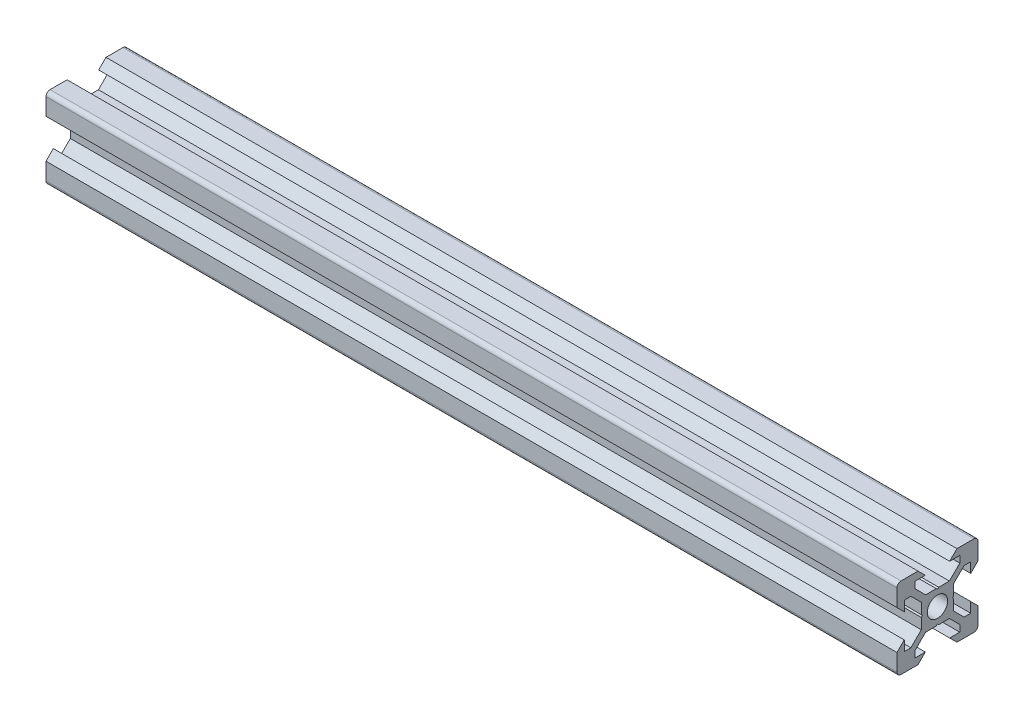
SolidWorks part; units mm, degrees
material "6063-T5"
material "6063-T5"
ref_plane "Plano frontal" through (0, 0, 0) normal (0, 0, 1) x (1, 0, 0)
ref_plane "Plano superior" through (0, 0, 0) normal (0, 1, 0) x (1, 0, 0)
ref_plane "Plano direito" through (0, 0, 0) normal (1, 0, 0) x (0, 0, -1)
sketch "Esboço1" plane through (0, 0, 0) normal (0, 0, 1) x (1, 0, 0)
  line L0 (0, 0) -> (210, 0)
  dimension "D1" = 210
other "Quadrado PF20-11 - PERFIL 2020 V-SLOT(1)"
ref_plane "Plano1" through (0, 0, 0) normal (1, 0, 0) x (0, 1, 0)
sketch "Sketch11" plane through (0, 0, 0) normal (1, 0, 0) x (0, 1, 0)
  line L0 (-4.8, 10) -> (-3, 8.2)
  line L1 (-3, 8.2) -> (-5.5, 8.2)
  line L2 (-5.5, 8.2) -> (-5.5, 6.5607)
  line L3 (-5.5, 6.5607) -> (-2.9393, 4)
  line L4 (-2.9393, 4) -> (-0.3, 4)
  line L5 (5.5, 6.5607) -> (2.9393, 4)
  line L6 (5.5, 8.2) -> (5.5, 6.5607)
  line L7 (3, 8.2) -> (5.5, 8.2)
  line L8 (4.8, 10) -> (3, 8.2)
  line L9 (-0.3, 4) -> (0, 3.7)
  line L10 (0.3, 4) -> (0, 3.7)
  line L11 (0.3, 4) -> (2.9393, 4)
  line L12 (9, 10) -> (4.8, 10)
  line L13 (10, 4.8) -> (8.2, 3)
  line L14 (10, 4.8) -> (10, 9)
  line L15 (8.2, 3) -> (8.2, 5.5)
  line L16 (8.2, 5.5) -> (6.5607, 5.5)
  line L17 (6.5607, 5.5) -> (4, 2.9393)
  line L18 (4.8, -10) -> (3, -8.2)
  line L19 (3, -8.2) -> (5.5, -8.2)
  line L20 (5.5, -8.2) -> (5.5, -6.5607)
  line L21 (5.5, -6.5607) -> (2.9393, -4)
  line L22 (2.9393, -4) -> (0.3, -4)
  line L23 (0.3, -4) -> (0, -3.7)
  line L24 (-0.3, -4) -> (0, -3.7)
  line L25 (-0.3, -4) -> (-2.9393, -4)
  line L26 (-5.5, -6.5607) -> (-2.9393, -4)
  line L27 (-5.5, -8.2) -> (-5.5, -6.5607)
  line L28 (-3, -8.2) -> (-5.5, -8.2)
  line L29 (-4.8, -10) -> (-3, -8.2)
  line L30 (-10, -4.8) -> (-10, -9)
  line L31 (-10, -4.8) -> (-8.2, -3)
  line L32 (-8.2, -3) -> (-8.2, -5.5)
  line L33 (-8.2, -5.5) -> (-6.5607, -5.5)
  line L34 (-6.5607, -5.5) -> (-4, -2.9393)
  line L35 (-4, -2.9393) -> (-4, -0.3)
  line L36 (-4, -0.3) -> (-3.7, 0)
  line L37 (-4, 0.3) -> (-3.7, 0)
  line L38 (-4, 0.3) -> (-4, 2.9393)
  line L39 (-6.5607, 5.5) -> (-4, 2.9393)
  line L40 (-8.2, 5.5) -> (-6.5607, 5.5)
  line L41 (-8.2, 3) -> (-8.2, 5.5)
  line L42 (-10, 4.8) -> (-8.2, 3)
  line L43 (-4.8, 10) -> (-9, 10)
  line L44 (4, 2.9393) -> (4, 0.3)
  line L45 (4, 0.3) -> (3.7, 0)
  line L46 (4, -0.3) -> (3.7, 0)
  line L47 (4, -0.3) -> (4, -2.9393)
  line L48 (6.5607, -5.5) -> (4, -2.9393)
  line L49 (8.2, -5.5) -> (6.5607, -5.5)
  line L50 (8.2, -3) -> (8.2, -5.5)
  line L51 (10, -4.8) -> (8.2, -3)
  line L52 (10, -9) -> (10, -4.8)
  line L53 (4.8, -10) -> (9, -10)
  line L106 (-10, 9) -> (-10, 4.8)
  line L107 (-9, -10) -> (-4.8, -10)
  arc A0 (10, 9) -> (9, 10) centre (9, 9) ccw
  arc A1 (9, -10) -> (10, -9) centre (9, -9) ccw
  arc A3 (-10, -9) -> (-9, -10) centre (-9, -9) ccw
  arc A4 (-9, 10) -> (-10, 9) centre (-9, 9) ccw
  circle A7 centre (0, 0) radius 2.5
  point P1 (-10, 10)
  point P3 (10, 10)
  point P4 (10, -10)
  point P68 (0, 0)
  point P70 (10, 0)
  point P71 (0, 0)
  point P72 (0, 0)
  point P113 (0, -10)
  point P114 (-10, -10)
  point P115 (-10, 0)
  point P116 (0, 10)
  point P118 (0, 0)
